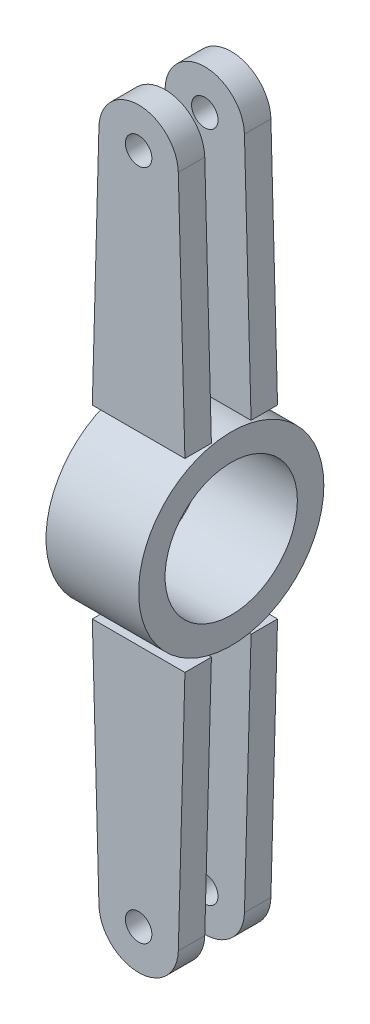
SolidWorks part; units mm, degrees
ref_plane "Front Plane" through (0, 0, 0) normal (0, 0, 1) x (1, 0, 0)
ref_plane "Top Plane" through (0, 0, 0) normal (0, 1, 0) x (1, 0, 0)
ref_plane "Right Plane" through (0, 0, 0) normal (1, 0, 0) x (0, 0, -1)
sketch "Sketch1" plane through (0, 0, 0) normal (1, 0, 0) x (0, 0, -1)
  circle A0 centre (0, 0) radius 25
  circle A1 centre (0, 0) radius 35
  dimension "D1" = 50
  dimension "D2" = 70
extrude "Boss-Extrude1" add sketch "Sketch1" along normal mid plane 35
sketch "Sketch2" plane through (0, 0, 0) normal (0, 0, 1) x (1, 0, 0)
  line L0 (-165.6074, 0) -> (171.1393, 0) construction
  line L1 (17.5, -35) -> (14.9945, -127.4066)
  line L2 (0, -35) -> (0, -127) construction
  line L3 (-17.5, -35) -> (-14.9945, -127.4066)
  line L4 (17.5, -35) -> (14.9945, -127.4066)
  line L9 (-17.5, -35) -> (-14.9945, -127.4066)
  line L11 (17.5, -35) -> (14.9945, -127.4066)
  line L12 (-17.5, -35) -> (-14.9945, -127.4066)
  line L13 (-17.5, -35) -> (17.5, -35) construction
  line L14 (-17.5, -35) -> (17.5, -35)
  line L16 (17.5, -35) -> (14.9945, -127.4066)
  line L17 (-17.5, -35) -> (-14.9945, -127.4066)
  line L18 (0, 35) -> (0, 127) construction
  line L19 (-17.5, 35) -> (-14.9945, 127.4066)
  line L20 (17.5, 35) -> (14.9945, 127.4066)
  line L21 (-17.5, 35) -> (17.5, 35)
  line L22 (-17.5, 35) -> (-14.9945, 127.4066)
  line L23 (17.5, 35) -> (14.9945, 127.4066)
  line L24 (-17.5, 35) -> (-14.9945, 127.4066)
  line L25 (17.5, 35) -> (14.9945, 127.4066)
  line L26 (-17.5, 35) -> (-14.9945, 127.4066)
  line L27 (17.5, 35) -> (14.9945, 127.4066)
  circle A3 centre (0, -127) radius 5
  arc A4 (-14.9945, -127.4066) -> (14.9945, -127.4066) centre (0, -127) ccw
  arc A5 (-14.9945, 127.4066) -> (14.9945, 127.4066) centre (0, 127) cw
  circle A6 centre (0, 127) radius 5
  dimension "D8" = 30
  dimension "D9" = 10
  dimension "D3" = 127
ref_plane "Plane1" through (0, 0, 7.5) normal (0, 0, 1) x (1, 0, 0)
sketch "Sketch4" plane through (0, 0, 7.5) normal (0, 0, 1) x (1, 0, 0)
  line L0 (-17.5, -35) -> (-14.9945, -127.4066) construction
  line L1 (17.5, -35) -> (14.9945, -127.4066) construction
  line L2 (-17.5, -35) -> (17.5, -35) construction
  line L6 (-17.5, -35) -> (-14.9945, -127.4066)
  line L7 (17.5, -35) -> (14.9945, -127.4066)
  line L8 (-17.5, -35) -> (17.5, -35)
  line L15 (-138.8873, 0) -> (132.3404, 0) construction
  line L16 (-17.5, 35) -> (17.5, 35)
  line L17 (17.5, 35) -> (14.9945, 127.4066)
  line L18 (-17.5, 35) -> (-14.9945, 127.4066)
  circle A0 centre (0, -127) radius 5 construction
  arc A1 (-14.9945, -127.4066) -> (14.9945, -127.4066) centre (0, -127) ccw construction
  circle A4 centre (0, -127) radius 5
  arc A5 (-14.9945, -127.4066) -> (14.9945, -127.4066) centre (0, -127) ccw
  arc A9 (-14.9945, 127.4066) -> (14.9945, 127.4066) centre (0, 127) cw
  circle A10 centre (0, 127) radius 5
ref_plane "Plane2" through (0, 0, -7.5) normal (0, 0, 1) x (1, 0, 0)
sketch "Sketch5" plane through (0, 0, -7.5) normal (0, 0, 1) x (1, 0, 0)
  line L0 (-17.5, -35) -> (-14.9945, -127.4066) construction
  line L1 (17.5, -35) -> (14.9945, -127.4066) construction
  line L2 (-17.5, -35) -> (17.5, -35) construction
  line L6 (-17.5, -35) -> (-14.9945, -127.4066)
  line L7 (17.5, -35) -> (14.9945, -127.4066)
  line L8 (-17.5, -35) -> (17.5, -35)
  line L13 (-108.2153, 0) -> (127.8859, 0) construction
  line L14 (-17.5, 35) -> (17.5, 35)
  line L15 (17.5, 35) -> (14.9945, 127.4066)
  line L16 (-17.5, 35) -> (-14.9945, 127.4066)
  circle A0 centre (0, -127) radius 5 construction
  arc A1 (-14.9945, -127.4066) -> (14.9945, -127.4066) centre (0, -127) ccw construction
  circle A4 centre (0, -127) radius 5
  arc A5 (-14.9945, -127.4066) -> (14.9945, -127.4066) centre (0, -127) ccw
  arc A8 (-14.9945, 127.4066) -> (14.9945, 127.4066) centre (0, 127) cw
  circle A9 centre (0, 127) radius 5
extrude "Boss-Extrude3" add sketch "Sketch5" against normal blind 10 separate body
extrude "Boss-Extrude5" add sketch "Sketch4" along normal blind 10 separate body
